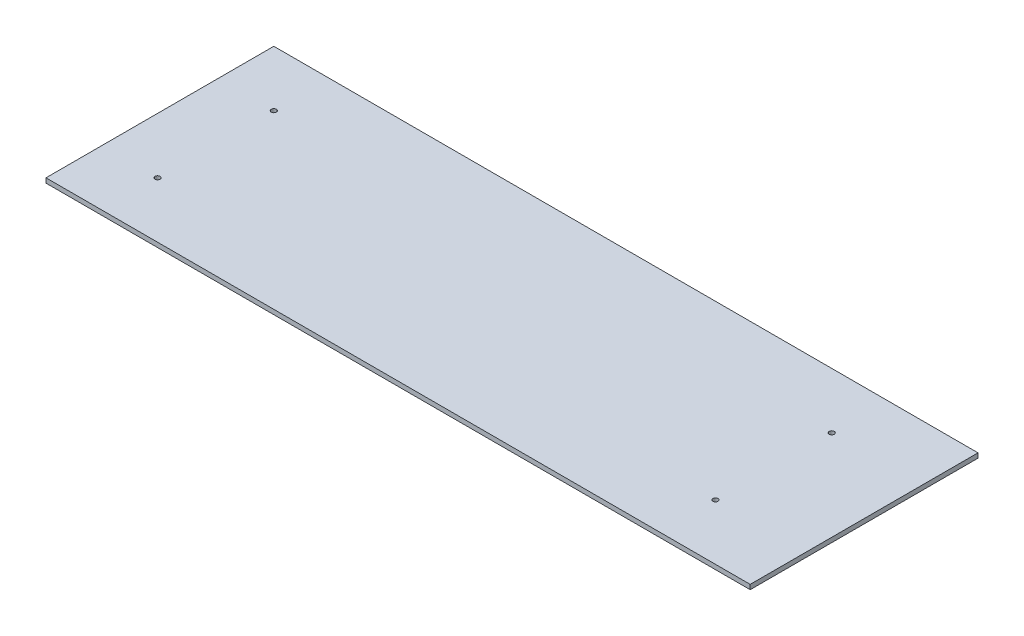
SolidWorks part; units mm, degrees
ref_plane "Front Plane" through (0, 0, 0) normal (0, 0, 1) x (1, 0, 0)
ref_plane "Top Plane" through (0, 0, 0) normal (0, 1, 0) x (1, 0, 0)
ref_plane "Right Plane" through (0, 0, 0) normal (1, 0, 0) x (0, 0, -1)
sketch "Sketch1" plane through (0, 0, 0) normal (0, 1, 0) x (1, 0, 0)
  line L0 (0, 0) -> (961.7927, 0)
  line L1 (0, 0) -> (0, 311.15)
  line L2 (0, 311.15) -> (961.7927, 311.15)
  line L3 (961.7927, 311.15) -> (961.7927, 0)
  dimension "D1" = 311.15
  dimension "D2" = 961.7927
extrude "Boss-Extrude1" add sketch "Sketch1" along normal blind 6.35
sketch "Sketch4" plane through (0, 6.35, 0) normal (0, 1, 0) x (1, 0, 0)
  line L1 (0, 155.575) -> (961.7927, 155.575) construction
  line L2 (0, 311.15) -> (0, 0) construction
  line L3 (961.7927, 0) -> (961.7927, 311.15) construction
  point P0 (76.2, 76.2)
  point P1 (76.2, 234.95)
  point P2 (838.2, 76.2)
  point P3 (838.2, 234.95)
  point P4 (76.2, 76.2)
  point P5 (76.2, 234.95)
  dimension "D1" = 158.75
  dimension "D2" = 158.75
hole_wizard "Tap Drill for 5/16-24 Tap1" positions "Sketch6" profile "Sketch5" hole size "5/16-24" standard "ANSI Inch" end condition through all
sketch "Sketch6" plane through (0, 6.35, 0) normal (0, 1, 0) x (1, 0, 0)
  point P0 (76.2, 76.2)
sketch "Sketch5" plane through (76.2, 6.35, -76.2) normal (1, 0, 0) x (0, 0, 1)
  line L0 (0, 0) -> (0, 6.35)
  line L1 (0, 6.35) -> (3.4544, 6.35)
  line L2 (3.4544, 6.35) -> (3.4544, 0)
  line L5 (3.4544, 0) -> (0, 0)
  line L11 (0, -6.35) -> (0, 107.95) construction
  dimension "Thru Hole Dia." = 6.9088
  dimension "Thru Hole Depth" = 6.35
hole_wizard "Tap Drill for 5/16-24 Tap2" positions "Sketch8" profile "Sketch7" hole size "5/16-24" standard "ANSI Inch" end condition through all
sketch "Sketch8" plane through (0, 6.35, 0) normal (0, 1, 0) x (1, 0, 0)
  point P0 (76.2, 234.95)
sketch "Sketch7" plane through (76.2, 6.35, -234.95) normal (1, 0, 0) x (0, 0, 1)
  line L0 (0, 0) -> (0, 6.35)
  line L1 (0, 6.35) -> (3.4544, 6.35)
  line L2 (3.4544, 6.35) -> (3.4544, 0)
  line L5 (3.4544, 0) -> (0, 0)
  line L11 (0, -6.35) -> (0, 107.95) construction
  dimension "Thru Hole Dia." = 6.9088
  dimension "Thru Hole Depth" = 6.35
hole_wizard "Tap Drill for 5/16-24 Tap3" positions "Sketch10" profile "Sketch9" hole size "5/16-24" standard "ANSI Inch" end condition through all
sketch "Sketch10" plane through (0, 6.35, 0) normal (0, 1, 0) x (1, 0, 0)
  point P0 (838.2, 76.2)
sketch "Sketch9" plane through (838.2, 6.35, -76.2) normal (1, 0, 0) x (0, 0, 1)
  line L0 (0, 0) -> (0, 6.35)
  line L1 (0, 6.35) -> (3.4544, 6.35)
  line L2 (3.4544, 6.35) -> (3.4544, 0)
  line L5 (3.4544, 0) -> (0, 0)
  line L11 (0, -6.35) -> (0, 107.95) construction
  dimension "Thru Hole Dia." = 6.9088
  dimension "Thru Hole Depth" = 6.35
hole_wizard "Tap Drill for 5/16-24 Tap4" positions "Sketch12" profile "Sketch11" hole size "5/16-24" standard "ANSI Inch" end condition through all
sketch "Sketch12" plane through (0, 6.35, 0) normal (0, 1, 0) x (1, 0, 0)
  point P0 (838.2, 234.95)
sketch "Sketch11" plane through (838.2, 6.35, -234.95) normal (1, 0, 0) x (0, 0, 1)
  line L0 (0, 0) -> (0, 6.35)
  line L1 (0, 6.35) -> (3.4544, 6.35)
  line L2 (3.4544, 6.35) -> (3.4544, 0)
  line L5 (3.4544, 0) -> (0, 0)
  line L11 (0, -6.35) -> (0, 107.95) construction
  dimension "Thru Hole Dia." = 6.9088
  dimension "Thru Hole Depth" = 6.35
sketch "Sketch13" [suppressed] plane through (0, 6.35, 0) normal (0, 1, 0) x (1, 0, 0)
  line L0 (0, 0) -> (25.6428, 0)
  line L1 (0, 0) -> (876.3, 0) construction
  line L2 (25.6428, 0) -> (25.6428, 260.35)
  line L3 (876.3, 260.35) -> (0, 260.35) construction
  line L4 (25.6428, 0) -> (101.6, 0)
  line L5 (101.6, 0) -> (101.6, 260.35)
  line L6 (0, 0) -> (0, 104.775)
  line L7 (0, 260.35) -> (0, 0) construction
  line L8 (0, 104.775) -> (876.3, 104.775)
  line L9 (0, 0) -> (0, 155.575)
  line L10 (0, 155.575) -> (876.3, 155.575)
  line L11 (101.6, 9.525) -> (152.4, 9.525)
  line L12 (152.4, 0) -> (152.4, 9.525)
  line L13 (152.4, 0) -> (152.4, 260.35)
  line L14 (152.4, 9.525) -> (723.9, 9.525)
  line L15 (723.9, 9.525) -> (723.9, 250.825)
  line L18 (152.4, 260.35) -> (152.4, 250.825)
  line L19 (723.9, 130.175) -> (774.7, 130.175)
sketch "Sketch15" plane through (0, 0, -311.15) normal (0, 0, -1) x (-1, 0, 0)
  line L4 (-961.7927, 0) -> (0, 0)
  line L5 (0, 0) -> (0, 6.35)
  line L6 (0, 6.35) -> (-961.7927, 6.35)
  line L7 (-961.7927, 6.35) -> (-961.7927, 0)
  line L8 (-961.7927, 0) -> (0, 0)
  line L9 (0, 0) -> (0, 6.35)
  line L10 (0, 6.35) -> (-961.7927, 6.35)
  line L11 (-961.7927, 6.35) -> (-961.7927, 0)
  dimension "D1" = 0
